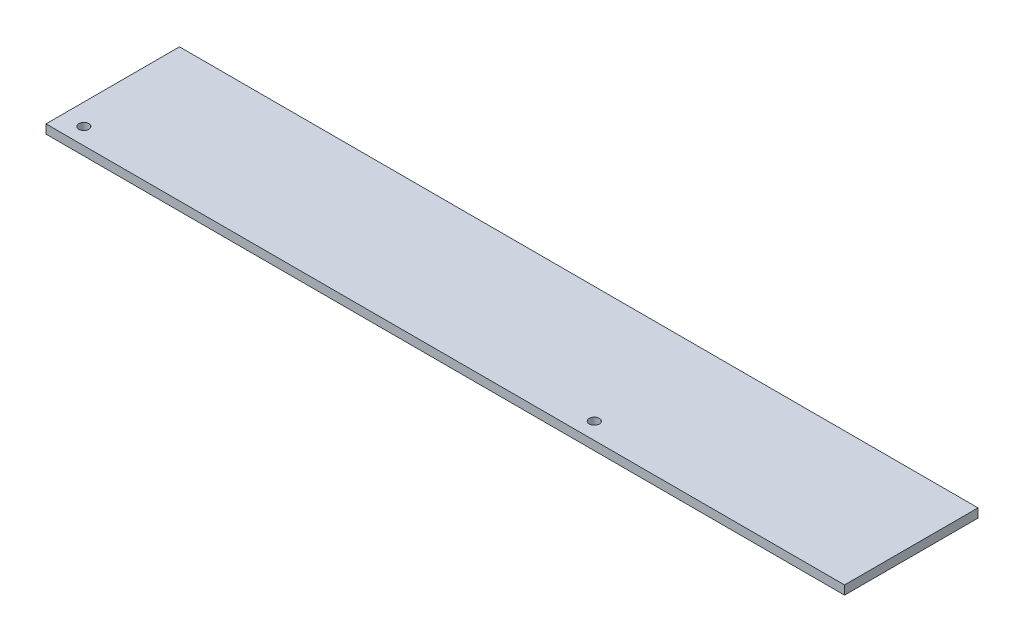
SolidWorks part; units mm, degrees
ref_plane "Спереди" through (0, 0, 0) normal (0, 0, 1) x (1, 0, 0)
ref_plane "Сверху" through (0, 0, 0) normal (0, 1, 0) x (1, 0, 0)
ref_plane "Справа" through (0, 0, 0) normal (1, 0, 0) x (0, 0, -1)
sketch "Эскиз1" plane through (0, 0, 0) normal (1, 0, 0) x (0, 0, -1)
  line L1 (-30, -2) -> (30, -2)
  line L2 (-30, -2) -> (-30, 2)
  line L3 (-30, 2) -> (30, 2)
  line L4 (30, -2) -> (30, 2)
  line L5 (-30, -2) -> (30, 2) construction
  line L6 (-30, 2) -> (30, -2) construction
  point P0 (0, 0)
  dimension "D1" = 4
  dimension "D2" = 60
extrude "Бобышка-Вытянуть1" add sketch "Эскиз1" along normal blind 359
sketch "Эскиз2" plane through (0, 2, 0) normal (0, 1, 0) x (1, 0, 0)
  line L0 (0, 30) -> (0, -30) construction
  line L2 (359, 30) -> (359, -30) construction
  line L3 (359, -30) -> (0, -30) construction
  circle A0 centre (9.5, -22.5) radius 2.25
  circle A1 centre (239, -22.5) radius 2.25
  dimension "D1" = 4.5
  dimension "D2" = 9.5
  dimension "D4" = 120
  dimension "D5" = 7.5
  dimension "D6" = 4.5
  dimension "D7" = 7.5
extrude "Вырез-Вытянуть1" cut sketch "Эскиз2" against normal through all
